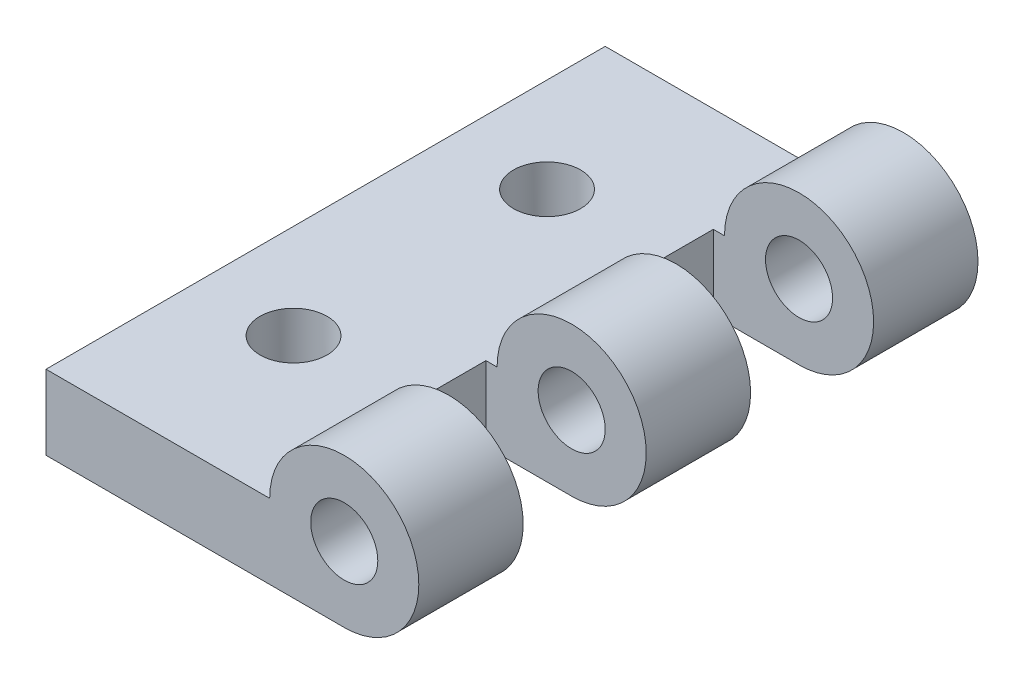
SolidWorks part; units mm, degrees
ref_plane "Front Plane" through (0, 0, 0) normal (0, 0, 1) x (1, 0, 0)
ref_plane "Top Plane" through (0, 0, 0) normal (0, 1, 0) x (1, 0, 0)
ref_plane "Right Plane" through (0, 0, 0) normal (1, 0, 0) x (0, 0, -1)
sketch "Sketch1" plane through (0, 0, 0) normal (0, 0, 1) x (1, 0, 0)
  line L0 (0, 5.08) -> (15.24, 5.08)
  line L1 (0, 0) -> (20.32, 0)
  line L2 (0, 0) -> (0, 5.08)
  circle A2 centre (20.32, 5.08) radius 2.286
  arc A3 (20.32, 0) -> (15.24, 5.08) centre (20.32, 5.08) ccw
  dimension "D1" = 10.16
  dimension "D2" = 4.572
  dimension "D3" = 5.08
  dimension "D4" = 15.24
extrude "Boss-Extrude1" add sketch "Sketch1" along normal blind 38.1
sketch "Sketch2" plane through (0, 5.08, 0) normal (0, 1, 0) x (1, 0, 0)
  line L0 (25.4, -38.1) -> (25.4, 0) construction
  line L1 (14.478, -7.112) -> (25.4, -7.112)
  line L2 (14.478, -7.112) -> (14.478, -15.494)
  line L3 (14.478, -15.494) -> (25.4, -15.494)
  line L4 (25.4, -7.112) -> (25.4, -15.494)
  line L5 (14.478, -7.112) -> (14.478, 0) construction
  line L6 (14.478, -22.606) -> (25.4, -22.606)
  line L7 (14.478, -22.606) -> (14.478, -30.988)
  line L8 (14.478, -30.988) -> (25.4, -30.988)
  line L9 (25.4, -22.606) -> (25.4, -30.988)
  line L10 (15.24, 0) -> (0, 0) construction
  line L11 (14.478, -15.494) -> (14.478, -22.606) construction
  line L12 (14.478, -30.988) -> (14.478, -38.1) construction
  line L13 (15.24, -38.1) -> (0, -38.1) construction
  line L14 (15.24, -38.1) -> (15.24, 0) construction
  dimension "D1" = 8.382
  dimension "D2" = 8.382
  dimension "D3" = 0.762
extrude "Cut-Extrude1" cut sketch "Sketch2" against normal through all both and the other way through all
sketch "Sketch3" plane through (0, 5.08, 0) normal (0, 1, 0) x (1, 0, 0)
  line L0 (6.4516, -25.4) -> (6.4516, -12.7) construction
  line L1 (6.4516, -8.128) -> (6.4516, 0) construction
  line L2 (15.24, 0) -> (0, 0) construction
  line L3 (6.4516, -29.972) -> (6.4516, -38.1) construction
  line L4 (15.24, -38.1) -> (0, -38.1) construction
  line L5 (15.24, -7.112) -> (15.24, 0) construction
  circle A0 centre (6.4516, -10.414) radius 2.286
  circle A1 centre (6.4516, -27.686) radius 2.286
  dimension "D1" = 4.572
  dimension "D2" = 12.7
  dimension "D3" = 8.7884
extrude "Cut-Extrude2" cut sketch "Sketch3" against normal through all and the other way through all
